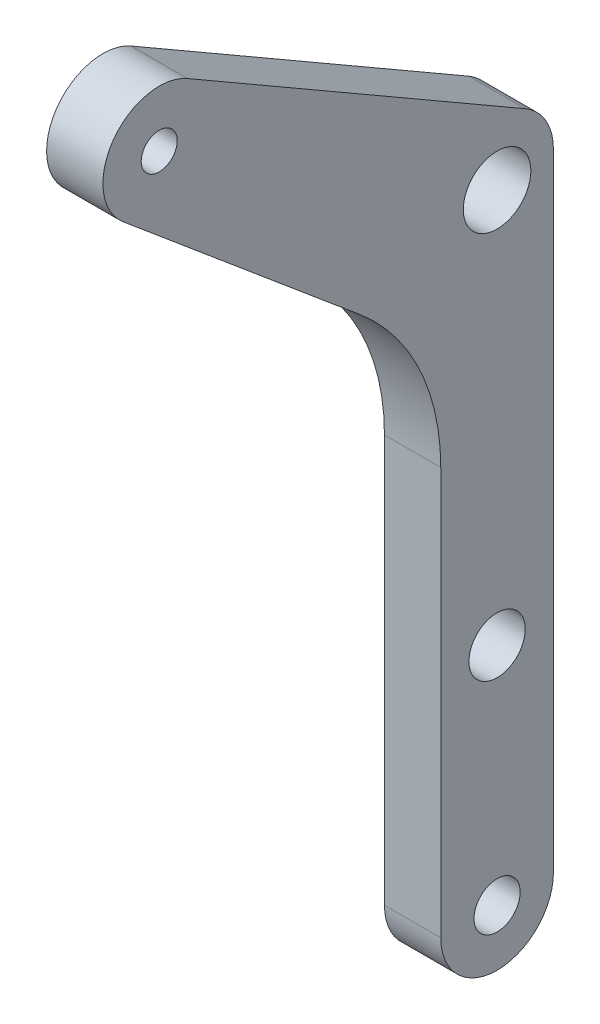
SolidWorks part; units mm, degrees
material "A-玻璃纤维"
ref_plane "前视基准面" through (0, 0, 0) normal (0, 0, 1) x (1, 0, 0)
ref_plane "上视基准面" through (0, 0, 0) normal (0, 1, 0) x (1, 0, 0)
ref_plane "右视基准面" through (0, 0, 0) normal (1, 0, 0) x (0, 0, -1)
sketch "草图1" plane through (0, 0, 0) normal (1, 0, 0) x (0, 0, -1)
  line L0 (0, 0) -> (0, 20) construction
  line L1 (0, 20) -> (0, 55) construction
  line L2 (5, 0) -> (5, 55.6795)
  line L3 (-5, 0) -> (-5, 52.7927) construction
  line L4 (2.5, 60.0096) -> (-27.5, 77.3301)
  line L5 (-34.9335, 70.0748) -> (-5, 52.7927) construction
  line L6 (-30, 73) -> (0, 73) construction
  line L7 (0, 73) -> (0, 55) construction
  line L8 (-33.2139, 69.1698) -> (-12.1442, 51.4902)
  line L9 (-5, 36.1693) -> (-5, 0)
  circle A0 centre (0, 0) radius 2.05
  circle A1 centre (0, 20) radius 2.5
  arc A2 (-5, 0) -> (5, 0) centre (0, 0) ccw
  circle A3 centre (0, 55) radius 3
  arc A4 (-27.5, 77.3301) -> (-33.2139, 69.1698) centre (-30, 73) ccw
  arc A5 (5, 55.6795) -> (2.5, 60.0096) centre (0, 55.6795) ccw
  arc A6 (-12.1442, 51.4902) -> (-5, 36.1693) centre (-25, 36.1693) cw
  circle A7 centre (-30, 73) radius 1.6
  point P22 (-5, 45.4955)
  dimension "D1" = 4.1
  dimension "D3" = 5
  dimension "D4" = 10
  dimension "D5" = 6
  dimension "D6" = 55
  dimension "D7" = 10
  dimension "D12" = 5
  dimension "D13" = 20
  dimension "D14" = 3.2
  dimension "D2" = 20
  dimension "D8" = 120
  dimension "D9" = 30
  dimension "D10" = 73
  dimension "D11" = 50
extrude "凸台-拉伸1" add sketch "草图1" along normal blind 5
sketch "草图2" plane through (0, 0, 0) normal (-1, 0, 0) x (0, 0, 1)
  circle A0 centre (30, 73) radius 2.25
  dimension "D1" = 4.5
extrude "切除-拉伸1" cut sketch "草图2" against normal blind 1.5
